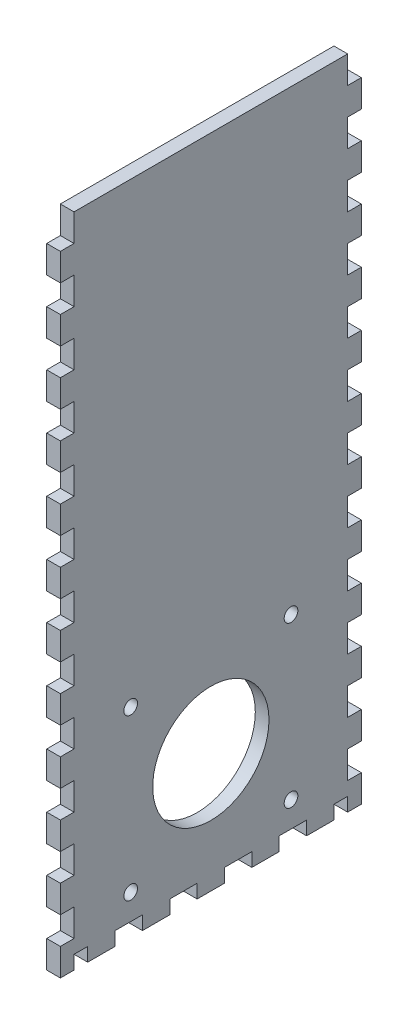
SolidWorks part; units mm, degrees
material "Acrylic (Medium-high impact)"
ref_plane "Front Plane" through (0, 0, 0) normal (0, 0, 1) x (1, 0, 0)
ref_plane "Top Plane" through (0, 0, 0) normal (0, 1, 0) x (1, 0, 0)
ref_plane "Right Plane" through (0, 0, 0) normal (1, 0, 0) x (0, 0, -1)
sketch "Sketch1" plane through (0, 0, 0) normal (0, 1, 0) x (1, 0, 0)
  line L1 (-136.525, 69.85) -> (136.525, 69.85)
  line L2 (-136.525, 69.85) -> (-136.525, -69.85)
  line L3 (-136.525, -69.85) -> (136.525, -69.85)
  line L4 (136.525, 69.85) -> (136.525, -69.85)
  point P4 (-136.525, 0)
  point P6 (0, 69.85)
  dimension "D1" = 139.7
  dimension "D2" = 273.05
extrude "Boss-Extrude1" add sketch "Sketch1" along normal blind 6.35
sketch "Sketch2" plane through (0, 6.35, 0) normal (0, 1, 0) x (1, 0, 0)
  line L0 (136.525, -69.85) -> (136.525, 69.85) construction
  line L1 (-136.525, 69.85) -> (136.525, 69.85)
  line L2 (-136.525, 69.85) -> (-136.525, -69.85)
  line L3 (-136.525, -69.85) -> (136.525, -69.85)
  line L4 (136.525, 69.85) -> (136.525, -69.85)
  line L5 (-136.525, -69.85) -> (136.525, -69.85) construction
  line L7 (-130.175, 63.5) -> (130.175, 63.5)
  line L8 (-130.175, 63.5) -> (-130.175, -63.5)
  line L9 (-130.175, -63.5) -> (130.175, -63.5)
  line L10 (130.175, 63.5) -> (130.175, -63.5)
  point P7 (-130.175, 0)
  point P14 (-136.525, 0)
  point P15 (0, -63.5)
  point P16 (0, -69.85)
  point P17 (130.175, 0)
  point P18 (136.525, 0)
  dimension "D1" = 6.35
  dimension "D2" = 6.35
extrude "Boss-Extrude2" add sketch "Sketch2" along normal blind 298.45
sketch "Sketch3" plane through (0, 0, 69.85) normal (0, 0, 1) x (1, 0, 0)
  line L0 (-25.273, 304.8) -> (-25.273, 0) construction
  line L2 (-130.175, 6.35) -> (130.175, 6.35) construction
  line L4 (-28.575, 283.21) -> (-28.575, 6.35)
  line L5 (-28.575, 6.35) -> (-21.971, 6.35)
  line L6 (-21.971, 292.354) -> (-21.971, 6.35)
  line L7 (-21.971, 292.354) -> (-41.529, 292.354)
  line L9 (-31.115, 285.75) -> (-41.529, 285.75)
  line L10 (-41.529, 292.354) -> (-41.529, 285.75)
  line L11 (-21.971, 101.6) -> (-9.271, 101.6) construction
  line L12 (-136.525, 0) -> (136.525, 0) construction
  line L13 (-12.446, 88.9) -> (-12.446, 101.6) construction
  line L14 (-15.621, 88.9) -> (-9.271, 88.9)
  line L15 (-15.621, 88.9) -> (-15.621, 71.9667)
  line L16 (-15.621, 71.9667) -> (-9.271, 71.9667)
  line L17 (-9.271, 88.9) -> (-9.271, 71.9667)
  line L18 (-15.621, 42.3333) -> (-9.271, 42.3333)
  line L19 (-15.621, 42.3333) -> (-15.621, 59.2667)
  line L20 (-15.621, 59.2667) -> (-9.271, 59.2667)
  line L21 (-9.271, 42.3333) -> (-9.271, 59.2667)
  line L26 (-15.621, 29.6333) -> (-9.271, 29.6333)
  line L27 (-15.621, 29.6333) -> (-15.621, 12.7)
  line L28 (-15.621, 12.7) -> (-9.271, 12.7)
  line L29 (-9.271, 29.6333) -> (-9.271, 12.7)
  line L30 (-12.446, 59.2667) -> (-12.446, 71.9667) construction
  line L31 (-12.446, 29.6333) -> (-12.446, 42.3333) construction
  line L32 (-12.446, 12.7) -> (-12.446, 0) construction
  line L33 (-136.525, 304.8) -> (136.525, 304.8) construction
  line L34 (-130.175, 304.8) -> (-130.175, 6.35) construction
  arc A0 (-28.575, 283.21) -> (-31.115, 285.75) centre (-31.115, 283.21) ccw
  point P2 (-65.1597, 304.8)
  point P5 (-25.273, 6.35)
  point P40 (0, 0)
  point P41 (0, 0)
  point P42 (0, 0)
  point P44 (-65.2242, 0)
  point P45 (-69.6985, 0)
  dimension "D5" = 2.54
  dimension "D1" = 6.604
  dimension "D2" = 12.954
  dimension "D3" = 6.604
  dimension "D4" = 286.004
  dimension "D6" = 101.6
  dimension "D7" = 12.7
  dimension "D8" = 12.7
  dimension "D9" = 6.35
  dimension "D10" = 101.6
extrude "Door Slot" cut sketch "Sketch3" against normal blind 12.7
sketch "Sketch4" plane through (0, 0, -63.5) normal (0, 0, 1) x (1, 0, 0)
  line L0 (-136.525, 304.8) -> (136.525, 304.8) construction
  line L1 (-47.879, 304.8) -> (-41.529, 304.8)
  line L2 (-47.879, 304.8) -> (-47.879, 6.35)
  line L3 (-47.879, 6.35) -> (-41.529, 6.35)
  line L4 (-41.529, 304.8) -> (-41.529, 6.35)
  line L5 (-18.796, 263.525) -> (-18.796, 247.65) construction
  line L6 (-41.529, 292.354) -> (-41.529, 285.75) construction
  line L7 (-21.971, 304.8) -> (-15.621, 304.8)
  line L8 (-21.971, 304.8) -> (-21.971, 6.35)
  line L9 (-21.971, 6.35) -> (-15.621, 6.35)
  line L10 (-15.621, 304.8) -> (-15.621, 6.35)
  line L11 (130.175, 6.35) -> (-130.175, 6.35) construction
  line L12 (-21.971, 6.35) -> (-21.971, 292.354) construction
  line L13 (-41.529, 304.8) -> (-47.879, 304.8)
  line L14 (-41.529, 304.8) -> (-41.529, 292.1)
  line L15 (-41.529, 292.1) -> (-47.879, 292.1)
  line L16 (-47.879, 304.8) -> (-47.879, 292.1)
  line L17 (-41.529, 276.225) -> (-47.879, 276.225)
  line L18 (-41.529, 276.225) -> (-41.529, 263.525)
  line L19 (-41.529, 263.525) -> (-47.879, 263.525)
  line L20 (-47.879, 276.225) -> (-47.879, 263.525)
  line L21 (-47.879, 6.35) -> (-41.529, 6.35)
  line L22 (-47.879, 6.35) -> (-47.879, 19.05)
  line L23 (-47.879, 19.05) -> (-41.529, 19.05)
  line L24 (-41.529, 6.35) -> (-41.529, 19.05)
  line L25 (-47.879, 34.925) -> (-41.529, 34.925)
  line L26 (-47.879, 34.925) -> (-47.879, 47.625)
  line L27 (-47.879, 47.625) -> (-41.529, 47.625)
  line L28 (-41.529, 34.925) -> (-41.529, 47.625)
  line L29 (-47.879, 92.075) -> (-41.529, 92.075)
  line L30 (-47.879, 92.075) -> (-47.879, 104.775)
  line L31 (-47.879, 104.775) -> (-41.529, 104.775)
  line L32 (-41.529, 92.075) -> (-41.529, 104.775)
  line L33 (-47.879, 149.225) -> (-41.529, 149.225)
  line L34 (-47.879, 149.225) -> (-47.879, 161.925)
  line L35 (-47.879, 161.925) -> (-41.529, 161.925)
  line L36 (-41.529, 149.225) -> (-41.529, 161.925)
  line L37 (-47.879, 177.8) -> (-41.529, 177.8)
  line L38 (-47.879, 177.8) -> (-47.879, 190.5)
  line L39 (-47.879, 190.5) -> (-41.529, 190.5)
  line L40 (-41.529, 177.8) -> (-41.529, 190.5)
  line L41 (-47.879, 206.375) -> (-41.529, 206.375)
  line L42 (-47.879, 206.375) -> (-47.879, 219.075)
  line L43 (-47.879, 219.075) -> (-41.529, 219.075)
  line L44 (-41.529, 206.375) -> (-41.529, 219.075)
  line L45 (-47.879, 234.95) -> (-41.529, 234.95)
  line L46 (-47.879, 234.95) -> (-47.879, 247.65)
  line L47 (-47.879, 247.65) -> (-41.529, 247.65)
  line L48 (-41.529, 234.95) -> (-41.529, 247.65)
  line L49 (-41.529, 133.35) -> (-47.879, 133.35)
  line L50 (-41.529, 133.35) -> (-41.529, 120.65)
  line L51 (-41.529, 120.65) -> (-47.879, 120.65)
  line L52 (-47.879, 133.35) -> (-47.879, 120.65)
  line L53 (-41.529, 76.2) -> (-47.879, 76.2)
  line L54 (-41.529, 76.2) -> (-41.529, 63.5)
  line L55 (-41.529, 63.5) -> (-47.879, 63.5)
  line L56 (-47.879, 76.2) -> (-47.879, 63.5)
  line L57 (-44.704, 304.8) -> (-44.704, 292.1) construction
  line L58 (-44.704, 292.1) -> (-44.704, 276.225) construction
  line L59 (-44.704, 276.225) -> (-44.704, 263.525) construction
  line L60 (-44.704, 247.65) -> (-44.704, 234.95) construction
  line L61 (-44.704, 234.95) -> (-44.704, 219.075) construction
  line L62 (-44.704, 219.075) -> (-44.704, 206.375) construction
  line L63 (-44.704, 206.375) -> (-44.704, 190.5) construction
  line L64 (-44.704, 190.5) -> (-44.704, 177.8) construction
  line L65 (-44.704, 177.8) -> (-44.704, 161.925) construction
  line L66 (-44.704, 161.925) -> (-44.704, 149.225) construction
  line L67 (-44.704, 133.35) -> (-44.704, 120.65) construction
  line L68 (-44.704, 120.65) -> (-44.704, 104.775) construction
  line L69 (-44.704, 104.775) -> (-44.704, 92.075) construction
  line L70 (-44.704, 92.075) -> (-44.704, 76.2) construction
  line L71 (-44.704, 76.2) -> (-44.704, 63.5) construction
  line L72 (-44.704, 63.5) -> (-44.704, 47.625) construction
  line L73 (-44.704, 47.625) -> (-44.704, 34.925) construction
  line L74 (-44.704, 34.925) -> (-44.704, 19.05) construction
  line L75 (-44.704, 19.05) -> (-44.704, 6.35) construction
  line L76 (-44.704, 149.225) -> (-44.704, 133.35) construction
  line L77 (-44.704, 263.525) -> (-44.704, 247.65) construction
  line L78 (-31.75, 304.8) -> (-31.75, 0) construction
  line L79 (136.525, 304.8) -> (-136.525, 304.8) construction
  line L80 (136.525, 0) -> (-136.525, 0) construction
  line L81 (-31.75, 8.3493) -> (-21.971, 8.3493) construction
  line L82 (-31.75, 8.3493) -> (-41.529, 8.3493) construction
  line L83 (-18.796, 149.225) -> (-18.796, 133.35) construction
  line L84 (-18.796, 19.05) -> (-18.796, 6.35) construction
  line L85 (-18.796, 34.925) -> (-18.796, 19.05) construction
  line L86 (-18.796, 47.625) -> (-18.796, 34.925) construction
  line L87 (-18.796, 63.5) -> (-18.796, 47.625) construction
  line L88 (-18.796, 76.2) -> (-18.796, 63.5) construction
  line L89 (-18.796, 92.075) -> (-18.796, 76.2) construction
  line L90 (-18.796, 104.775) -> (-18.796, 92.075) construction
  line L91 (-18.796, 120.65) -> (-18.796, 104.775) construction
  line L92 (-18.796, 133.35) -> (-18.796, 120.65) construction
  line L93 (-18.796, 161.925) -> (-18.796, 149.225) construction
  line L94 (-18.796, 177.8) -> (-18.796, 161.925) construction
  line L95 (-18.796, 190.5) -> (-18.796, 177.8) construction
  line L96 (-18.796, 206.375) -> (-18.796, 190.5) construction
  line L97 (-18.796, 219.075) -> (-18.796, 206.375) construction
  line L98 (-18.796, 234.95) -> (-18.796, 219.075) construction
  line L99 (-18.796, 247.65) -> (-18.796, 234.95) construction
  line L100 (-18.796, 276.225) -> (-18.796, 263.525) construction
  line L101 (-18.796, 292.1) -> (-18.796, 276.225) construction
  line L102 (-18.796, 304.8) -> (-18.796, 292.1) construction
  line L103 (-15.621, 76.2) -> (-15.621, 63.5)
  line L104 (-21.971, 63.5) -> (-15.621, 63.5)
  line L105 (-21.971, 76.2) -> (-21.971, 63.5)
  line L106 (-21.971, 76.2) -> (-15.621, 76.2)
  line L107 (-15.621, 133.35) -> (-15.621, 120.65)
  line L108 (-21.971, 120.65) -> (-15.621, 120.65)
  line L109 (-21.971, 133.35) -> (-21.971, 120.65)
  line L110 (-21.971, 133.35) -> (-15.621, 133.35)
  line L111 (-21.971, 234.95) -> (-21.971, 247.65)
  line L112 (-15.621, 247.65) -> (-21.971, 247.65)
  line L113 (-15.621, 234.95) -> (-15.621, 247.65)
  line L114 (-15.621, 234.95) -> (-21.971, 234.95)
  line L115 (-21.971, 206.375) -> (-21.971, 219.075)
  line L116 (-15.621, 219.075) -> (-21.971, 219.075)
  line L117 (-15.621, 206.375) -> (-15.621, 219.075)
  line L118 (-15.621, 206.375) -> (-21.971, 206.375)
  line L119 (-21.971, 177.8) -> (-21.971, 190.5)
  line L120 (-15.621, 190.5) -> (-21.971, 190.5)
  line L121 (-15.621, 177.8) -> (-15.621, 190.5)
  line L122 (-15.621, 177.8) -> (-21.971, 177.8)
  line L123 (-21.971, 149.225) -> (-21.971, 161.925)
  line L124 (-15.621, 161.925) -> (-21.971, 161.925)
  line L125 (-15.621, 149.225) -> (-15.621, 161.925)
  line L126 (-15.621, 149.225) -> (-21.971, 149.225)
  line L127 (-21.971, 92.075) -> (-21.971, 104.775)
  line L128 (-15.621, 104.775) -> (-21.971, 104.775)
  line L129 (-15.621, 92.075) -> (-15.621, 104.775)
  line L130 (-15.621, 92.075) -> (-21.971, 92.075)
  line L131 (-21.971, 34.925) -> (-21.971, 47.625)
  line L132 (-15.621, 47.625) -> (-21.971, 47.625)
  line L133 (-15.621, 34.925) -> (-15.621, 47.625)
  line L134 (-15.621, 34.925) -> (-21.971, 34.925)
  line L135 (-21.971, 6.35) -> (-21.971, 19.05)
  line L136 (-15.621, 19.05) -> (-21.971, 19.05)
  line L137 (-15.621, 6.35) -> (-15.621, 19.05)
  line L138 (-15.621, 6.35) -> (-21.971, 6.35)
  line L139 (-15.621, 276.225) -> (-15.621, 263.525)
  line L140 (-21.971, 263.525) -> (-15.621, 263.525)
  line L141 (-21.971, 276.225) -> (-21.971, 263.525)
  line L142 (-21.971, 276.225) -> (-15.621, 276.225)
  line L143 (-15.621, 304.8) -> (-15.621, 292.1)
  line L144 (-21.971, 292.1) -> (-15.621, 292.1)
  line L145 (-21.971, 304.8) -> (-21.971, 292.1)
  line L146 (-21.971, 304.8) -> (-15.621, 304.8)
  line L147 (-21.971, 304.8) -> (-21.971, 6.35)
  line L148 (-15.621, 6.35) -> (-21.971, 6.35)
  line L149 (-15.621, 304.8) -> (-15.621, 6.35)
  line L150 (-15.621, 304.8) -> (-21.971, 304.8)
  point P14 (-41.529, 289.052)
  dimension "D1" = 6.35
  dimension "D2" = 12.7
extrude "Door Guide Holes" cut sketch "Sketch4" against normal up to next contours L17 L4 L15 L2 | L2 L47 L4 L19 | L45 L2 L43 L4 | L41 L2 L39 L4 | L37 L2 L35 L4 | L49 L4 L33 L2 | L4 L51 L2 L31 | L53 L4 L29 L2 | L4 L55 L2 L27 | L25 L2 L23 L4
ref_plane "Plane1" through (-31.75, 0, 0) normal (-1, 0, 0) x (0, 0, 1)
mirror "Mirror1" about plane through (-31.75, 0, 0) normal (-1, 0, 0) of "Door Guide Holes"
sketch "Lever Holes" plane through (0, 0, 69.85) normal (0, 0, 1) x (1, 0, 0)
  line L0 (49.276, 31.75) -> (58.928, 31.75)
  line L1 (49.276, 31.75) -> (49.276, 25.4)
  line L2 (49.276, 25.4) -> (58.928, 25.4)
  line L3 (58.928, 31.75) -> (58.928, 25.4)
  line L4 (36.1315, 19.05) -> (42.4815, 19.05)
  line L5 (36.1315, 19.05) -> (36.1315, 12.7)
  line L6 (36.1315, 12.7) -> (42.4815, 12.7)
  line L7 (42.4815, 19.05) -> (42.4815, 12.7)
  line L8 (65.7225, 19.05) -> (72.0725, 19.05)
  line L9 (65.7225, 19.05) -> (65.7225, 12.7)
  line L10 (65.7225, 12.7) -> (72.0725, 12.7)
  line L11 (72.0725, 19.05) -> (72.0725, 12.7)
  line L12 (42.4815, 15.875) -> (65.7225, 15.875) construction
  line L13 (-136.525, 0) -> (136.525, 0) construction
  line L14 (-21.971, 6.35) -> (130.175, 6.35) construction
  line L15 (130.175, 6.35) -> (-130.175, 6.35) construction
  point P12 (54.102, 15.875)
  point P13 (54.102, 25.4)
  point P14 (39.3065, 12.7)
  point P24 (54.102, 6.35)
  point P25 (0, 0)
  dimension "D1" = 9.652
  dimension "D2" = 6.35
  dimension "D3" = 6.35
  dimension "D4" = 6.35
  dimension "D5" = 23.241
  dimension "D6" = 25.4
  dimension "D7" = 12.7
extrude "Cut-Extrude1" cut sketch "Lever Holes" against normal through all
sketch "Sketch7" plane through (136.525, 0, 0) normal (1, 0, 0) x (0, 0, -1)
  line L0 (-37.211, 92.583) -> (37.211, 92.583)
  line L1 (-37.211, 92.583) -> (-37.211, 18.161)
  line L2 (-37.211, 18.161) -> (37.211, 18.161)
  line L3 (37.211, 92.583) -> (37.211, 18.161)
  line L4 (-69.85, 0) -> (69.85, 0) construction
  circle A0 centre (0, 55.372) radius 26.9875
  circle A1 centre (-37.211, 92.583) radius 3.175
  circle A2 centre (37.211, 92.583) radius 3.175
  circle A3 centre (-37.211, 18.161) radius 3.175
  circle A4 centre (37.211, 18.161) radius 3.175
  point P9 (0, 18.161)
  point P10 (-37.211, 55.372)
  point P12 (43.7877, 25.7461)
  point P15 (0, 0)
  dimension "D3" = 53.975
  dimension "D4" = 6.35
  dimension "D1" = 74.422
  dimension "D2" = 55.372
extrude "Cut-Extrude2" cut sketch "Sketch7" against normal up to next contours A0 | L0 A1 L1 | L1 A1 L0 | L3 A2 L0 | L0 A2 L3 | L2 A3 L1 | L1 A3 L2 | L2 A4 L3 | L3 A4 L2
sketch "Sketch8" plane through (-136.525, 0, 0) normal (-1, 0, 0) x (0, 0, 1)
  line L0 (-69.85, 0) -> (69.85, 0) construction
  circle A0 centre (0, 19.05) radius 3.175
  point P2 (0, 0)
  point P6 (0, 0)
  dimension "D1" = 6.35
  dimension "D2" = 19.05
extrude "Cut-Extrude3" cut sketch "Sketch8" against normal up to next
sketch "Bottom" plane through (0, 0, 0) normal (0, -1, 0) x (1, 0, 0)
  line L0 (-130.175, 63.5) -> (130.175, 63.5) construction
  line L1 (-136.525, 69.85) -> (-122.1539, 69.85)
  line L2 (-136.525, 69.85) -> (-136.525, 63.5)
  line L3 (-136.525, 63.5) -> (-122.1539, 63.5)
  line L4 (-122.1539, 69.85) -> (-122.1539, 63.5)
  line L5 (-122.1539, 69.85) -> (-107.7829, 69.85)
  line L6 (-122.1539, 69.85) -> (-122.1539, 63.5)
  line L7 (-122.1539, 63.5) -> (-107.7829, 63.5)
  line L8 (-107.7829, 69.85) -> (-107.7829, 63.5)
  line L9 (-107.7829, 69.85) -> (-93.4118, 69.85)
  line L10 (-107.7829, 69.85) -> (-107.7829, 63.5)
  line L11 (-107.7829, 63.5) -> (-93.4118, 63.5)
  line L12 (-93.4118, 69.85) -> (-93.4118, 63.5)
  line L13 (-93.4118, 69.85) -> (-79.0408, 69.85)
  line L14 (-93.4118, 69.85) -> (-93.4118, 63.5)
  line L15 (-93.4118, 63.5) -> (-79.0408, 63.5)
  line L16 (-79.0408, 69.85) -> (-79.0408, 63.5)
  line L17 (-136.525, 69.85) -> (136.525, 69.85) construction
  line L18 (-41.529, 63.5) -> (-21.971, 63.5) construction
  line L19 (-79.0408, 69.85) -> (-64.6697, 69.85)
  line L20 (-79.0408, 69.85) -> (-79.0408, 63.5)
  line L21 (-79.0408, 63.5) -> (-64.6697, 63.5)
  line L22 (-64.6697, 69.85) -> (-64.6697, 63.5)
  line L23 (-64.6697, 69.85) -> (-50.2987, 69.85)
  line L24 (-64.6697, 69.85) -> (-64.6697, 63.5)
  line L25 (-64.6697, 63.5) -> (-50.2987, 63.5)
  line L26 (-50.2987, 69.85) -> (-50.2987, 63.5)
  line L27 (-50.2987, 69.85) -> (-35.9276, 69.85)
  line L28 (-50.2987, 69.85) -> (-50.2987, 63.5)
  line L29 (-50.2987, 63.5) -> (-35.9276, 63.5)
  line L30 (-35.9276, 69.85) -> (-35.9276, 63.5)
  line L31 (-35.9276, 69.85) -> (-21.5566, 69.85)
  line L32 (-35.9276, 69.85) -> (-35.9276, 63.5)
  line L33 (-35.9276, 63.5) -> (-21.5566, 63.5)
  line L34 (-21.5566, 69.85) -> (-21.5566, 63.5)
  line L36 (-21.5566, 69.85) -> (-7.1855, 69.85)
  line L37 (-21.5566, 69.85) -> (-21.5566, 63.5)
  line L38 (-21.5566, 63.5) -> (-7.1855, 63.5)
  line L39 (-7.1855, 69.85) -> (-7.1855, 63.5)
  line L40 (-7.1855, 69.85) -> (7.1855, 69.85)
  line L41 (-7.1855, 69.85) -> (-7.1855, 63.5)
  line L42 (-7.1855, 63.5) -> (7.1855, 63.5)
  line L43 (7.1855, 69.85) -> (7.1855, 63.5)
  line L44 (7.1855, 69.85) -> (21.5566, 69.85)
  line L45 (7.1855, 69.85) -> (7.1855, 63.5)
  line L46 (7.1855, 63.5) -> (21.5566, 63.5)
  line L47 (21.5566, 69.85) -> (21.5566, 63.5)
  line L48 (21.5566, 69.85) -> (35.9276, 69.85)
  line L49 (21.5566, 69.85) -> (21.5566, 63.5)
  line L50 (21.5566, 63.5) -> (35.9276, 63.5)
  line L51 (35.9276, 69.85) -> (35.9276, 63.5)
  line L52 (35.9276, 69.85) -> (50.2987, 69.85)
  line L53 (35.9276, 69.85) -> (35.9276, 63.5)
  line L54 (35.9276, 63.5) -> (50.2987, 63.5)
  line L55 (50.2987, 69.85) -> (50.2987, 63.5)
  line L56 (50.2987, 69.85) -> (64.6697, 69.85)
  line L57 (50.2987, 69.85) -> (50.2987, 63.5)
  line L58 (50.2987, 63.5) -> (64.6697, 63.5)
  line L59 (64.6697, 69.85) -> (64.6697, 63.5)
  line L60 (64.6697, 69.85) -> (79.0408, 69.85)
  line L61 (64.6697, 69.85) -> (64.6697, 63.5)
  line L62 (64.6697, 63.5) -> (79.0408, 63.5)
  line L63 (79.0408, 69.85) -> (79.0408, 63.5)
  line L64 (79.0408, 69.85) -> (93.4118, 69.85)
  line L65 (79.0408, 69.85) -> (79.0408, 63.5)
  line L66 (79.0408, 63.5) -> (93.4118, 63.5)
  line L67 (93.4118, 69.85) -> (93.4118, 63.5)
  line L68 (93.4118, 69.85) -> (107.7829, 69.85)
  line L69 (93.4118, 69.85) -> (93.4118, 63.5)
  line L70 (93.4118, 63.5) -> (107.7829, 63.5)
  line L71 (107.7829, 69.85) -> (107.7829, 63.5)
  line L72 (107.7829, 69.85) -> (122.1539, 69.85)
  line L73 (107.7829, 69.85) -> (107.7829, 63.5)
  line L74 (107.7829, 63.5) -> (122.1539, 63.5)
  line L75 (122.1539, 69.85) -> (122.1539, 63.5)
  line L76 (-130.175, -63.5) -> (-130.175, 63.5) construction
  line L77 (-136.525, 69.85) -> (-130.175, 69.85)
  line L78 (-136.525, 69.85) -> (-136.525, 57.15)
  line L79 (-136.525, 57.15) -> (-130.175, 57.15)
  line L80 (-130.175, 69.85) -> (-130.175, 57.15)
  line L82 (-136.525, 57.15) -> (-130.175, 57.15)
  line L83 (-136.525, 57.15) -> (-136.525, 44.45)
  line L84 (-136.525, 44.45) -> (-130.175, 44.45)
  line L85 (-130.175, 57.15) -> (-130.175, 44.45)
  line L86 (-136.525, 44.45) -> (-130.175, 44.45)
  line L87 (-136.525, 44.45) -> (-136.525, 31.75)
  line L88 (-136.525, 31.75) -> (-130.175, 31.75)
  line L89 (-130.175, 44.45) -> (-130.175, 31.75)
  line L90 (-136.525, 31.75) -> (-130.175, 31.75)
  line L91 (-136.525, 31.75) -> (-136.525, 19.05)
  line L92 (-136.525, 19.05) -> (-130.175, 19.05)
  line L93 (-130.175, 31.75) -> (-130.175, 19.05)
  line L94 (-136.525, 19.05) -> (-130.175, 19.05)
  line L95 (-136.525, 19.05) -> (-136.525, 6.35)
  line L96 (-136.525, 6.35) -> (-130.175, 6.35)
  line L97 (-130.175, 19.05) -> (-130.175, 6.35)
  line L98 (-136.525, 6.35) -> (-130.175, 6.35)
  line L99 (-136.525, 6.35) -> (-136.525, -6.35)
  line L100 (-136.525, -6.35) -> (-130.175, -6.35)
  line L101 (-130.175, 6.35) -> (-130.175, -6.35)
  line L102 (-136.525, -6.35) -> (-130.175, -6.35)
  line L103 (-136.525, -6.35) -> (-136.525, -19.05)
  line L104 (-136.525, -19.05) -> (-130.175, -19.05)
  line L105 (-130.175, -6.35) -> (-130.175, -19.05)
  line L106 (-136.525, -19.05) -> (-130.175, -19.05)
  line L107 (-136.525, -19.05) -> (-136.525, -31.75)
  line L108 (-136.525, -31.75) -> (-130.175, -31.75)
  line L109 (-130.175, -19.05) -> (-130.175, -31.75)
  line L110 (-136.525, -31.75) -> (-130.175, -31.75)
  line L111 (-136.525, -31.75) -> (-136.525, -44.45)
  line L112 (-136.525, -44.45) -> (-130.175, -44.45)
  line L113 (-130.175, -31.75) -> (-130.175, -44.45)
  line L114 (-136.525, -44.45) -> (-130.175, -44.45)
  line L115 (-136.525, -44.45) -> (-136.525, -57.15)
  line L116 (-136.525, -57.15) -> (-130.175, -57.15)
  line L117 (-130.175, -44.45) -> (-130.175, -57.15)
  line L118 (136.525, 69.85) -> (136.525, -69.85) construction
  line L119 (122.1539, 69.85) -> (136.525, 69.85)
  line L120 (122.1539, 69.85) -> (122.1539, 63.5)
  line L121 (122.1539, 63.5) -> (136.525, 63.5)
  line L122 (136.525, 69.85) -> (136.525, 63.5)
  line L123 (136.525, -69.85) -> (-136.525, -69.85) construction
  line L124 (-136.525, -57.15) -> (-130.175, -57.15)
  line L125 (-136.525, -57.15) -> (-136.525, -69.85)
  line L126 (-136.525, -69.85) -> (-130.175, -69.85)
  line L127 (-130.175, -57.15) -> (-130.175, -69.85)
  line L128 (150.1775, 0) -> (-150.1775, 0) construction
  line L129 (136.525, -69.85) -> (136.525, -63.5)
  line L130 (122.1539, -63.5) -> (136.525, -63.5)
  line L131 (122.1539, -69.85) -> (136.525, -69.85)
  line L132 (122.1539, -69.85) -> (122.1539, -63.5)
  line L133 (107.7829, -63.5) -> (122.1539, -63.5)
  line L134 (107.7829, -69.85) -> (122.1539, -69.85)
  line L135 (107.7829, -69.85) -> (107.7829, -63.5)
  line L136 (93.4118, -63.5) -> (107.7829, -63.5)
  line L137 (93.4118, -69.85) -> (107.7829, -69.85)
  line L138 (93.4118, -69.85) -> (93.4118, -63.5)
  line L139 (79.0408, -63.5) -> (93.4118, -63.5)
  line L140 (79.0408, -69.85) -> (93.4118, -69.85)
  line L141 (79.0408, -69.85) -> (79.0408, -63.5)
  line L142 (64.6697, -63.5) -> (79.0408, -63.5)
  line L143 (64.6697, -69.85) -> (79.0408, -69.85)
  line L144 (50.2987, -63.5) -> (64.6697, -63.5)
  line L145 (64.6697, -69.85) -> (64.6697, -63.5)
  line L146 (50.2987, -69.85) -> (64.6697, -69.85)
  line L147 (50.2987, -69.85) -> (50.2987, -63.5)
  line L148 (35.9276, -63.5) -> (50.2987, -63.5)
  line L149 (35.9276, -69.85) -> (50.2987, -69.85)
  line L150 (35.9276, -69.85) -> (35.9276, -63.5)
  line L151 (21.5566, -63.5) -> (35.9276, -63.5)
  line L152 (21.5566, -69.85) -> (35.9276, -69.85)
  line L153 (21.5566, -69.85) -> (21.5566, -63.5)
  line L154 (7.1855, -69.85) -> (21.5566, -69.85)
  line L155 (7.1855, -63.5) -> (21.5566, -63.5)
  line L156 (7.1855, -69.85) -> (7.1855, -63.5)
  line L157 (-7.1855, -63.5) -> (7.1855, -63.5)
  line L158 (-7.1855, -69.85) -> (7.1855, -69.85)
  line L159 (-21.5566, -63.5) -> (-7.1855, -63.5)
  line L160 (-7.1855, -69.85) -> (-7.1855, -63.5)
  line L161 (-21.5566, -69.85) -> (-7.1855, -69.85)
  line L162 (-21.5566, -69.85) -> (-21.5566, -63.5)
  line L163 (-35.9276, -63.5) -> (-21.5566, -63.5)
  line L164 (-35.9276, -69.85) -> (-21.5566, -69.85)
  line L165 (-35.9276, -69.85) -> (-35.9276, -63.5)
  line L166 (-50.2987, -63.5) -> (-35.9276, -63.5)
  line L167 (-50.2987, -69.85) -> (-35.9276, -69.85)
  line L168 (-50.2987, -69.85) -> (-50.2987, -63.5)
  line L169 (-64.6697, -69.85) -> (-50.2987, -69.85)
  line L170 (-64.6697, -63.5) -> (-50.2987, -63.5)
  line L171 (-79.0408, -63.5) -> (-64.6697, -63.5)
  line L172 (-64.6697, -69.85) -> (-64.6697, -63.5)
  line L173 (-79.0408, -69.85) -> (-64.6697, -69.85)
  line L174 (-93.4118, -69.85) -> (-79.0408, -69.85)
  line L175 (-93.4118, -63.5) -> (-79.0408, -63.5)
  line L176 (-79.0408, -69.85) -> (-79.0408, -63.5)
  line L177 (-107.7829, -69.85) -> (-107.7829, -63.5)
  line L178 (-107.7829, -69.85) -> (-93.4118, -69.85)
  line L179 (-93.4118, -69.85) -> (-93.4118, -63.5)
  line L180 (-107.7829, -63.5) -> (-93.4118, -63.5)
  line L181 (-122.1539, -63.5) -> (-107.7829, -63.5)
  line L182 (-122.1539, -69.85) -> (-107.7829, -69.85)
  line L183 (-122.1539, -69.85) -> (-122.1539, -63.5)
  line L184 (-136.525, -69.85) -> (-122.1539, -69.85)
  line L185 (-136.525, -69.85) -> (-136.525, -63.5)
  line L186 (-136.525, -63.5) -> (-122.1539, -63.5)
  line L187 (0, -76.835) -> (0, 76.835) construction
  line L188 (136.525, -69.85) -> (130.175, -69.85)
  line L189 (130.175, -57.15) -> (130.175, -69.85)
  line L190 (136.525, -57.15) -> (136.525, -69.85)
  line L191 (136.525, -57.15) -> (130.175, -57.15)
  line L192 (130.175, -44.45) -> (130.175, -57.15)
  line L193 (136.525, -44.45) -> (136.525, -57.15)
  line L194 (136.525, -44.45) -> (130.175, -44.45)
  line L195 (130.175, -31.75) -> (130.175, -44.45)
  line L196 (136.525, -31.75) -> (136.525, -44.45)
  line L197 (136.525, -31.75) -> (130.175, -31.75)
  line L198 (136.525, -19.05) -> (136.525, -31.75)
  line L199 (130.175, -19.05) -> (130.175, -31.75)
  line L200 (130.175, -6.35) -> (130.175, -19.05)
  line L201 (136.525, -6.35) -> (136.525, -19.05)
  line L202 (136.525, -19.05) -> (130.175, -19.05)
  line L203 (136.525, -6.35) -> (130.175, -6.35)
  line L204 (130.175, 6.35) -> (130.175, -6.35)
  line L205 (136.525, 6.35) -> (136.525, -6.35)
  line L206 (136.525, 6.35) -> (130.175, 6.35)
  line L207 (130.175, 19.05) -> (130.175, 6.35)
  line L208 (136.525, 19.05) -> (136.525, 6.35)
  line L209 (136.525, 19.05) -> (130.175, 19.05)
  line L210 (136.525, 31.75) -> (130.175, 31.75)
  line L211 (136.525, 44.45) -> (130.175, 44.45)
  line L212 (136.525, 57.15) -> (130.175, 57.15)
  line L213 (130.175, 31.75) -> (130.175, 19.05)
  line L214 (136.525, 31.75) -> (136.525, 19.05)
  line L215 (130.175, 44.45) -> (130.175, 31.75)
  line L216 (136.525, 44.45) -> (136.525, 31.75)
  line L217 (130.175, 57.15) -> (130.175, 44.45)
  line L218 (136.525, 57.15) -> (136.525, 44.45)
  line L219 (130.175, 69.85) -> (130.175, 57.15)
  line L220 (136.525, 69.85) -> (136.525, 57.15)
sketch "Front/Back" plane through (0, 0, 69.85) normal (0, 0, 1) x (1, 0, 0)
  line L0 (-130.175, 6.35) -> (-28.575, 6.35) construction
  line L1 (-136.525, 0) -> (-122.1539, 0)
  line L2 (-136.525, 0) -> (-136.525, 6.35)
  line L3 (-136.525, 6.35) -> (-122.1539, 6.35)
  line L4 (-122.1539, 0) -> (-122.1539, 6.35)
  line L5 (-136.525, 0) -> (136.525, 0) construction
  line L6 (-107.7829, 0) -> (-93.4118, 0) construction
  line L7 (-122.1539, 6.35) -> (-107.7829, 6.35)
  line L8 (-122.1539, 6.35) -> (-122.1539, 0)
  line L9 (-122.1539, 0) -> (-107.7829, 0)
  line L10 (-107.7829, 6.35) -> (-107.7829, 0)
  line L11 (-79.0408, 0) -> (-64.6697, 0) construction
  line L12 (-107.7829, 6.35) -> (-93.4118, 6.35)
  line L13 (-107.7829, 6.35) -> (-107.7829, 0)
  line L14 (-107.7829, 0) -> (-93.4118, 0)
  line L15 (-93.4118, 6.35) -> (-93.4118, 0)
  line L16 (-93.4118, 6.35) -> (-79.0408, 6.35)
  line L17 (-93.4118, 6.35) -> (-93.4118, 0)
  line L18 (-93.4118, 0) -> (-79.0408, 0)
  line L19 (-79.0408, 6.35) -> (-79.0408, 0)
  line L20 (-64.6697, 0) -> (-50.2987, 0) construction
  line L21 (-79.0408, 6.35) -> (-64.6697, 6.35)
  line L22 (-79.0408, 6.35) -> (-79.0408, 0)
  line L23 (-79.0408, 0) -> (-64.6697, 0)
  line L24 (-64.6697, 6.35) -> (-64.6697, 0)
  line L25 (-64.6697, 6.35) -> (-50.2987, 6.35)
  line L26 (-64.6697, 6.35) -> (-64.6697, 0)
  line L27 (-64.6697, 0) -> (-50.2987, 0)
  line L28 (-50.2987, 6.35) -> (-50.2987, 0)
  line L29 (-50.2987, 0) -> (-35.9276, 0) construction
  line L30 (-50.2987, 6.35) -> (-35.9276, 6.35)
  line L31 (-50.2987, 6.35) -> (-50.2987, 0)
  line L32 (-50.2987, 0) -> (-35.9276, 0)
  line L33 (-35.9276, 6.35) -> (-35.9276, 0)
  line L34 (-21.5566, 0) -> (-7.1855, 0) construction
  line L35 (-35.9276, 6.35) -> (-21.5566, 6.35)
  line L36 (-35.9276, 6.35) -> (-35.9276, 0)
  line L37 (-35.9276, 0) -> (-21.5566, 0)
  line L38 (-21.5566, 6.35) -> (-21.5566, 0)
  line L39 (7.1855, 0) -> (21.5566, 0) construction
  line L40 (-21.5566, 6.35) -> (-7.1855, 6.35)
  line L41 (-21.5566, 6.35) -> (-21.5566, 0)
  line L42 (-21.5566, 0) -> (-7.1855, 0)
  line L43 (-7.1855, 6.35) -> (-7.1855, 0)
  line L44 (-7.1855, 6.35) -> (7.1855, 6.35)
  line L45 (-7.1855, 6.35) -> (-7.1855, 0)
  line L46 (-7.1855, 0) -> (7.1855, 0)
  line L47 (7.1855, 6.35) -> (7.1855, 0)
  line L48 (7.1855, 0) -> (21.5566, 0) construction
  line L49 (35.9276, 0) -> (50.2987, 0) construction
  line L50 (7.1855, 6.35) -> (21.5566, 6.35)
  line L51 (7.1855, 6.35) -> (7.1855, 0)
  line L52 (7.1855, 0) -> (21.5566, 0)
  line L53 (21.5566, 6.35) -> (21.5566, 0)
  line L54 (21.5566, 6.35) -> (35.9276, 6.35)
  line L55 (21.5566, 6.35) -> (21.5566, 0)
  line L56 (21.5566, 0) -> (35.9276, 0)
  line L57 (35.9276, 6.35) -> (35.9276, 0)
  line L58 (64.6697, 0) -> (79.0408, 0) construction
  line L59 (35.9276, 6.35) -> (50.2987, 6.35)
  line L60 (35.9276, 6.35) -> (35.9276, 0)
  line L61 (35.9276, 0) -> (50.2987, 0)
  line L62 (50.2987, 6.35) -> (50.2987, 0)
  line L63 (50.2987, 6.35) -> (64.6697, 6.35)
  line L64 (50.2987, 6.35) -> (50.2987, 0)
  line L65 (50.2987, 0) -> (64.6697, 0)
  line L66 (64.6697, 6.35) -> (64.6697, 0)
  line L67 (50.2987, 0) -> (64.6697, 0) construction
  line L68 (93.4118, 0) -> (107.7829, 0) construction
  line L69 (64.6697, 6.35) -> (79.0408, 6.35)
  line L70 (64.6697, 6.35) -> (64.6697, 0)
  line L71 (64.6697, 0) -> (79.0408, 0)
  line L72 (79.0408, 6.35) -> (79.0408, 0)
  line L73 (79.0408, 6.35) -> (93.4118, 6.35)
  line L74 (79.0408, 6.35) -> (79.0408, 0)
  line L75 (79.0408, 0) -> (93.4118, 0)
  line L76 (93.4118, 6.35) -> (93.4118, 0)
  line L77 (107.7829, 0) -> (122.1539, 0) construction
  line L78 (93.4118, 6.35) -> (107.7829, 6.35)
  line L79 (93.4118, 6.35) -> (93.4118, 0)
  line L80 (93.4118, 0) -> (107.7829, 0)
  line L81 (107.7829, 6.35) -> (107.7829, 0)
  line L82 (107.7829, 0) -> (122.1539, 0) construction
  line L84 (107.7829, 6.35) -> (122.1539, 6.35)
  line L85 (107.7829, 6.35) -> (107.7829, 0)
  line L86 (107.7829, 0) -> (122.1539, 0)
  line L87 (122.1539, 6.35) -> (122.1539, 0)
  line L88 (122.1539, 6.35) -> (136.525, 6.35)
  line L89 (122.1539, 6.35) -> (122.1539, 0)
  line L90 (122.1539, 0) -> (136.525, 0)
  line L91 (136.525, 6.35) -> (136.525, 0)
  line L92 (-130.175, 304.8) -> (-130.175, 6.35) construction
  line L93 (-136.525, 0) -> (-130.175, 0)
  line L94 (-136.525, 0) -> (-136.525, 12.7)
  line L95 (-136.525, 12.7) -> (-130.175, 12.7)
  line L96 (-130.175, 0) -> (-130.175, 12.7)
  line L97 (-136.525, 304.8) -> (-136.525, 0) construction
  line L98 (-136.525, 12.7) -> (-130.175, 12.7)
  line L99 (-136.525, 12.7) -> (-136.525, 25.4)
  line L100 (-136.525, 25.4) -> (-130.175, 25.4)
  line L101 (-130.175, 12.7) -> (-130.175, 25.4)
  line L102 (-136.525, 25.4) -> (-130.175, 25.4)
  line L103 (-136.525, 25.4) -> (-136.525, 38.1)
  line L104 (-136.525, 38.1) -> (-130.175, 38.1)
  line L105 (-130.175, 25.4) -> (-130.175, 38.1)
  line L106 (-136.525, 38.1) -> (-130.175, 38.1)
  line L107 (-136.525, 38.1) -> (-136.525, 50.8)
  line L108 (-136.525, 50.8) -> (-130.175, 50.8)
  line L109 (-130.175, 38.1) -> (-130.175, 50.8)
  line L110 (-136.525, 50.8) -> (-130.175, 50.8)
  line L111 (-136.525, 50.8) -> (-136.525, 63.5)
  line L112 (-136.525, 63.5) -> (-130.175, 63.5)
  line L113 (-130.175, 50.8) -> (-130.175, 63.5)
  line L114 (-136.525, 63.5) -> (-130.175, 63.5)
  line L115 (-136.525, 63.5) -> (-136.525, 76.2)
  line L116 (-136.525, 76.2) -> (-130.175, 76.2)
  line L117 (-130.175, 63.5) -> (-130.175, 76.2)
  line L118 (-136.525, 76.2) -> (-130.175, 76.2)
  line L119 (-136.525, 76.2) -> (-136.525, 88.9)
  line L120 (-136.525, 88.9) -> (-130.175, 88.9)
  line L121 (-130.175, 76.2) -> (-130.175, 88.9)
  line L122 (-136.525, 88.9) -> (-130.175, 88.9)
  line L123 (-136.525, 88.9) -> (-136.525, 101.6)
  line L124 (-136.525, 101.6) -> (-130.175, 101.6)
  line L125 (-130.175, 88.9) -> (-130.175, 101.6)
  line L126 (-136.525, 101.6) -> (-130.175, 101.6)
  line L127 (-136.525, 101.6) -> (-136.525, 114.3)
  line L128 (-136.525, 114.3) -> (-130.175, 114.3)
  line L129 (-130.175, 101.6) -> (-130.175, 114.3)
  line L130 (-136.525, 114.3) -> (-130.175, 114.3)
  line L131 (-136.525, 114.3) -> (-136.525, 127)
  line L132 (-136.525, 127) -> (-130.175, 127)
  line L133 (-130.175, 114.3) -> (-130.175, 127)
  line L134 (-136.525, 127) -> (-130.175, 127)
  line L135 (-136.525, 127) -> (-136.525, 139.7)
  line L136 (-136.525, 139.7) -> (-130.175, 139.7)
  line L137 (-130.175, 127) -> (-130.175, 139.7)
  line L138 (-136.525, 139.7) -> (-130.175, 139.7)
  line L139 (-136.525, 139.7) -> (-136.525, 152.4)
  line L140 (-136.525, 152.4) -> (-130.175, 152.4)
  line L141 (-130.175, 139.7) -> (-130.175, 152.4)
  line L142 (-136.525, 152.4) -> (-130.175, 152.4)
  line L143 (-136.525, 152.4) -> (-136.525, 165.1)
  line L144 (-136.525, 165.1) -> (-130.175, 165.1)
  line L145 (-130.175, 152.4) -> (-130.175, 165.1)
  line L146 (-136.525, 165.1) -> (-130.175, 165.1)
  line L147 (-136.525, 165.1) -> (-136.525, 177.8)
  line L148 (-136.525, 177.8) -> (-130.175, 177.8)
  line L149 (-130.175, 165.1) -> (-130.175, 177.8)
  line L150 (-136.525, 177.8) -> (-130.175, 177.8)
  line L151 (-136.525, 177.8) -> (-136.525, 190.5)
  line L152 (-136.525, 190.5) -> (-130.175, 190.5)
  line L153 (-130.175, 177.8) -> (-130.175, 190.5)
  line L154 (-136.525, 190.5) -> (-130.175, 190.5)
  line L155 (-136.525, 190.5) -> (-136.525, 203.2)
  line L156 (-136.525, 203.2) -> (-130.175, 203.2)
  line L157 (-130.175, 190.5) -> (-130.175, 203.2)
  line L158 (-136.525, 203.2) -> (-130.175, 203.2)
  line L159 (-136.525, 203.2) -> (-136.525, 215.9)
  line L160 (-136.525, 215.9) -> (-130.175, 215.9)
  line L161 (-130.175, 203.2) -> (-130.175, 215.9)
  line L162 (-136.525, 215.9) -> (-130.175, 215.9)
  line L163 (-136.525, 215.9) -> (-136.525, 228.6)
  line L164 (-136.525, 228.6) -> (-130.175, 228.6)
  line L165 (-130.175, 215.9) -> (-130.175, 228.6)
  line L166 (-136.525, 228.6) -> (-130.175, 228.6)
  line L167 (-136.525, 228.6) -> (-136.525, 241.3)
  line L168 (-136.525, 241.3) -> (-130.175, 241.3)
  line L169 (-130.175, 228.6) -> (-130.175, 241.3)
  line L170 (-136.525, 241.3) -> (-130.175, 241.3)
  line L171 (-136.525, 241.3) -> (-136.525, 254)
  line L172 (-136.525, 254) -> (-130.175, 254)
  line L173 (-130.175, 241.3) -> (-130.175, 254)
  line L174 (-136.525, 254) -> (-130.175, 254)
  line L175 (-136.525, 254) -> (-136.525, 266.7)
  line L176 (-136.525, 266.7) -> (-130.175, 266.7)
  line L177 (-130.175, 254) -> (-130.175, 266.7)
  line L178 (-136.525, 266.7) -> (-130.175, 266.7)
  line L179 (-136.525, 266.7) -> (-136.525, 279.4)
  line L180 (-136.525, 279.4) -> (-130.175, 279.4)
  line L181 (-130.175, 266.7) -> (-130.175, 279.4)
  line L182 (-136.525, 279.4) -> (-130.175, 279.4)
  line L183 (-136.525, 279.4) -> (-136.525, 292.1)
  line L184 (-136.525, 292.1) -> (-130.175, 292.1)
  line L185 (-130.175, 279.4) -> (-130.175, 292.1)
  line L186 (-136.525, 292.1) -> (-130.175, 292.1)
  line L187 (-136.525, 292.1) -> (-136.525, 304.8)
  line L188 (-136.525, 304.8) -> (-130.175, 304.8)
  line L189 (-130.175, 292.1) -> (-130.175, 304.8)
  line L190 (-136.525, 304.8) -> (-130.175, 304.8)
  line L194 (-136.525, 304.8) -> (136.525, 304.8) construction
  line L195 (0, -76.835) -> (0, 76.835) construction
  line L196 (136.525, 304.8) -> (130.175, 304.8)
  line L197 (130.175, 292.1) -> (130.175, 304.8)
  line L198 (136.525, 304.8) -> (130.175, 304.8)
  line L199 (136.525, 292.1) -> (136.525, 304.8)
  line L200 (136.525, 292.1) -> (130.175, 292.1)
  line L201 (130.175, 279.4) -> (130.175, 292.1)
  line L202 (136.525, 292.1) -> (130.175, 292.1)
  line L203 (136.525, 279.4) -> (136.525, 292.1)
  line L204 (136.525, 279.4) -> (130.175, 279.4)
  line L205 (130.175, 266.7) -> (130.175, 279.4)
  line L206 (136.525, 279.4) -> (130.175, 279.4)
  line L207 (136.525, 266.7) -> (136.525, 279.4)
  line L208 (136.525, 266.7) -> (130.175, 266.7)
  line L209 (130.175, 254) -> (130.175, 266.7)
  line L210 (136.525, 266.7) -> (130.175, 266.7)
  line L211 (136.525, 254) -> (136.525, 266.7)
  line L212 (136.525, 254) -> (130.175, 254)
  line L213 (130.175, 241.3) -> (130.175, 254)
  line L214 (136.525, 254) -> (130.175, 254)
  line L215 (136.525, 241.3) -> (136.525, 254)
  line L216 (136.525, 241.3) -> (130.175, 241.3)
  line L217 (130.175, 228.6) -> (130.175, 241.3)
  line L218 (136.525, 241.3) -> (130.175, 241.3)
  line L219 (136.525, 228.6) -> (136.525, 241.3)
  line L220 (136.525, 228.6) -> (130.175, 228.6)
  line L221 (130.175, 215.9) -> (130.175, 228.6)
  line L222 (136.525, 228.6) -> (130.175, 228.6)
  line L223 (136.525, 215.9) -> (136.525, 228.6)
  line L224 (136.525, 215.9) -> (130.175, 215.9)
  line L225 (130.175, 203.2) -> (130.175, 215.9)
  line L226 (136.525, 215.9) -> (130.175, 215.9)
  line L227 (136.525, 203.2) -> (136.525, 215.9)
  line L228 (136.525, 203.2) -> (130.175, 203.2)
  line L229 (130.175, 190.5) -> (130.175, 203.2)
  line L230 (136.525, 203.2) -> (130.175, 203.2)
  line L231 (136.525, 190.5) -> (136.525, 203.2)
  line L232 (136.525, 190.5) -> (130.175, 190.5)
  line L233 (130.175, 177.8) -> (130.175, 190.5)
  line L234 (136.525, 190.5) -> (130.175, 190.5)
  line L235 (136.525, 177.8) -> (136.525, 190.5)
  line L236 (136.525, 177.8) -> (130.175, 177.8)
  line L237 (130.175, 165.1) -> (130.175, 177.8)
  line L238 (136.525, 177.8) -> (130.175, 177.8)
  line L239 (136.525, 165.1) -> (136.525, 177.8)
  line L240 (136.525, 165.1) -> (130.175, 165.1)
  line L241 (130.175, 152.4) -> (130.175, 165.1)
  line L242 (136.525, 165.1) -> (130.175, 165.1)
  line L243 (136.525, 152.4) -> (136.525, 165.1)
  line L244 (136.525, 152.4) -> (130.175, 152.4)
  line L245 (130.175, 139.7) -> (130.175, 152.4)
  line L246 (136.525, 152.4) -> (130.175, 152.4)
  line L247 (136.525, 139.7) -> (136.525, 152.4)
  line L248 (136.525, 139.7) -> (130.175, 139.7)
  line L249 (130.175, 127) -> (130.175, 139.7)
  line L250 (136.525, 139.7) -> (130.175, 139.7)
  line L251 (136.525, 127) -> (136.525, 139.7)
  line L252 (136.525, 127) -> (130.175, 127)
  line L253 (130.175, 114.3) -> (130.175, 127)
  line L254 (136.525, 127) -> (130.175, 127)
  line L255 (136.525, 114.3) -> (136.525, 127)
  line L256 (136.525, 114.3) -> (130.175, 114.3)
  line L257 (130.175, 101.6) -> (130.175, 114.3)
  line L258 (136.525, 114.3) -> (130.175, 114.3)
  line L259 (136.525, 101.6) -> (136.525, 114.3)
  line L260 (136.525, 101.6) -> (130.175, 101.6)
  line L261 (130.175, 88.9) -> (130.175, 101.6)
  line L262 (136.525, 101.6) -> (130.175, 101.6)
  line L263 (136.525, 88.9) -> (136.525, 101.6)
  line L264 (136.525, 88.9) -> (130.175, 88.9)
  line L265 (130.175, 76.2) -> (130.175, 88.9)
  line L266 (136.525, 88.9) -> (130.175, 88.9)
  line L267 (136.525, 76.2) -> (136.525, 88.9)
  line L268 (136.525, 76.2) -> (130.175, 76.2)
  line L269 (130.175, 63.5) -> (130.175, 76.2)
  line L270 (136.525, 76.2) -> (130.175, 76.2)
  line L271 (136.525, 63.5) -> (136.525, 76.2)
  line L272 (136.525, 63.5) -> (130.175, 63.5)
  line L273 (130.175, 50.8) -> (130.175, 63.5)
  line L274 (136.525, 63.5) -> (130.175, 63.5)
  line L275 (136.525, 50.8) -> (136.525, 63.5)
  line L276 (136.525, 50.8) -> (130.175, 50.8)
  line L277 (130.175, 38.1) -> (130.175, 50.8)
  line L278 (136.525, 50.8) -> (130.175, 50.8)
  line L279 (136.525, 38.1) -> (136.525, 50.8)
  line L280 (136.525, 38.1) -> (130.175, 38.1)
  line L281 (130.175, 25.4) -> (130.175, 38.1)
  line L282 (136.525, 38.1) -> (130.175, 38.1)
  line L283 (136.525, 25.4) -> (136.525, 38.1)
  line L284 (136.525, 25.4) -> (130.175, 25.4)
  line L285 (130.175, 12.7) -> (130.175, 25.4)
  line L286 (136.525, 25.4) -> (130.175, 25.4)
  line L287 (136.525, 12.7) -> (136.525, 25.4)
  line L288 (136.525, 12.7) -> (130.175, 12.7)
  line L289 (130.175, 0) -> (130.175, 12.7)
  line L290 (136.525, 12.7) -> (130.175, 12.7)
  line L291 (136.525, 0) -> (136.525, 12.7)
  line L292 (136.525, 0) -> (130.175, 0)
  line L293 (136.525, 0) -> (136.525, 6.35)
  point P123 (-136.525, 299.0254)
  point P125 (-130.175, 299.1915)
  point P126 (0, 0)
  point P127 (0, 0)
sketch "Left/Right" plane through (-136.525, 0, 0) normal (-1, 0, 0) x (0, 0, 1)
  line L0 (57.15, 0) -> (44.45, 0) construction
  line L8 (57.15, 0) -> (57.15, 6.35)
  line L9 (57.15, 6.35) -> (44.45, 6.35)
  line L10 (57.15, 6.35) -> (57.15, 0)
  line L11 (57.15, 0) -> (44.45, 0)
  line L12 (44.45, 6.35) -> (44.45, 0)
  line L13 (-69.85, 0) -> (69.85, 0) construction
  line L14 (44.45, 0) -> (31.75, 0) construction
  line L15 (44.45, 6.35) -> (31.75, 6.35)
  line L16 (44.45, 6.35) -> (44.45, 0)
  line L17 (44.45, 0) -> (31.75, 0)
  line L18 (31.75, 6.35) -> (31.75, 0)
  line L19 (31.75, 0) -> (19.05, 0) construction
  line L20 (31.75, 6.35) -> (19.05, 6.35)
  line L21 (31.75, 6.35) -> (31.75, 0)
  line L22 (31.75, 0) -> (19.05, 0)
  line L23 (19.05, 6.35) -> (19.05, 0)
  line L24 (19.05, 0) -> (6.35, 0) construction
  line L25 (19.05, 6.35) -> (6.35, 6.35)
  line L26 (19.05, 6.35) -> (19.05, 0)
  line L27 (19.05, 0) -> (6.35, 0)
  line L28 (6.35, 6.35) -> (6.35, 0)
  line L29 (6.35, 0) -> (-6.35, 0) construction
  line L30 (6.35, 6.35) -> (-6.35, 6.35)
  line L31 (6.35, 6.35) -> (6.35, 0)
  line L32 (6.35, 0) -> (-6.35, 0)
  line L33 (-6.35, 6.35) -> (-6.35, 0)
  line L34 (-6.35, 0) -> (-19.05, 0) construction
  line L35 (-6.35, 6.35) -> (-19.05, 6.35)
  line L36 (-6.35, 6.35) -> (-6.35, 0)
  line L37 (-6.35, 0) -> (-19.05, 0)
  line L38 (-19.05, 6.35) -> (-19.05, 0)
  line L39 (-19.05, 0) -> (-31.75, 0) construction
  line L40 (-19.05, 6.35) -> (-31.75, 6.35)
  line L41 (-19.05, 6.35) -> (-19.05, 0)
  line L42 (-19.05, 0) -> (-31.75, 0)
  line L43 (-31.75, 6.35) -> (-31.75, 0)
  line L44 (-19.05, 0) -> (-31.75, 0) construction
  line L45 (-31.75, 0) -> (-44.45, 0) construction
  line L46 (-31.75, 6.35) -> (-44.45, 6.35)
  line L47 (-31.75, 6.35) -> (-31.75, 0)
  line L48 (-31.75, 0) -> (-44.45, 0)
  line L49 (-44.45, 6.35) -> (-44.45, 0)
  line L50 (69.85, 304.8) -> (69.85, 0) construction
  line L51 (-44.45, 6.35) -> (-57.15, 6.35)
  line L52 (-44.45, 6.35) -> (-44.45, 0)
  line L53 (-44.45, 0) -> (-57.15, 0)
  line L55 (-69.85, 0) -> (-63.5, 0) construction
  line L57 (-57.15, 6.35) -> (-57.15, 0)
  line L60 (-69.85, 0) -> (-63.5, 0) construction
  line L61 (69.85, 0) -> (57.15, 0) construction
  line L63 (-69.85, 6.35) -> (-69.85, 0)
  line L65 (57.15, 6.35) -> (69.85, 6.35)
  line L66 (57.15, 6.35) -> (57.15, 0)
  line L67 (57.15, 0) -> (69.85, 0)
  line L68 (69.85, 6.35) -> (69.85, 0)
  line L69 (69.85, 165.1) -> (69.85, 177.8) construction
  line L70 (63.5, 12.7) -> (69.85, 12.7)
  line L71 (63.5, 12.7) -> (63.5, 25.4)
  line L72 (63.5, 25.4) -> (69.85, 25.4)
  line L73 (-57.15, 0) -> (-69.85, 0)
  line L74 (-69.85, 6.35) -> (-57.15, 6.35)
  line L75 (-57.15, 0) -> (-69.85, 0) construction
  line L76 (69.85, 12.7) -> (69.85, 25.4)
  line L77 (69.85, 0) -> (63.5, 0)
  line L78 (69.85, 0) -> (69.85, 12.7)
  line L79 (69.85, 12.7) -> (63.5, 12.7)
  line L80 (63.5, 0) -> (63.5, 12.7)
  line L81 (63.5, 25.4) -> (69.85, 25.4)
  line L82 (63.5, 25.4) -> (63.5, 38.1)
  line L83 (63.5, 38.1) -> (69.85, 38.1)
  line L84 (69.85, 25.4) -> (69.85, 38.1)
  line L85 (63.5, 38.1) -> (69.85, 38.1)
  line L86 (63.5, 38.1) -> (63.5, 50.8)
  line L87 (63.5, 50.8) -> (69.85, 50.8)
  line L88 (69.85, 38.1) -> (69.85, 50.8)
  line L89 (63.5, 50.8) -> (69.85, 50.8)
  line L90 (63.5, 50.8) -> (63.5, 63.5)
  line L91 (63.5, 63.5) -> (69.85, 63.5)
  line L92 (69.85, 50.8) -> (69.85, 63.5)
  line L93 (63.5, 63.5) -> (69.85, 63.5)
  line L94 (63.5, 63.5) -> (63.5, 76.2)
  line L95 (63.5, 76.2) -> (69.85, 76.2)
  line L96 (69.85, 63.5) -> (69.85, 76.2)
  line L97 (63.5, 76.2) -> (69.85, 76.2)
  line L98 (63.5, 76.2) -> (63.5, 88.9)
  line L99 (63.5, 88.9) -> (69.85, 88.9)
  line L100 (69.85, 76.2) -> (69.85, 88.9)
  line L101 (63.5, 88.9) -> (69.85, 88.9)
  line L102 (63.5, 88.9) -> (63.5, 101.6)
  line L103 (63.5, 101.6) -> (69.85, 101.6)
  line L104 (69.85, 88.9) -> (69.85, 101.6)
  line L105 (63.5, 101.6) -> (69.85, 101.6)
  line L106 (63.5, 101.6) -> (63.5, 114.3)
  line L107 (63.5, 114.3) -> (69.85, 114.3)
  line L108 (69.85, 101.6) -> (69.85, 114.3)
  line L109 (63.5, 114.3) -> (69.85, 114.3)
  line L110 (63.5, 114.3) -> (63.5, 127)
  line L111 (63.5, 127) -> (69.85, 127)
  line L112 (69.85, 114.3) -> (69.85, 127)
  line L113 (63.5, 127) -> (69.85, 127)
  line L114 (63.5, 127) -> (63.5, 139.7)
  line L115 (63.5, 139.7) -> (69.85, 139.7)
  line L116 (69.85, 127) -> (69.85, 139.7)
  line L117 (63.5, 139.7) -> (69.85, 139.7)
  line L118 (63.5, 139.7) -> (63.5, 152.4)
  line L119 (63.5, 152.4) -> (69.85, 152.4)
  line L120 (69.85, 139.7) -> (69.85, 152.4)
  line L121 (63.5, 152.4) -> (69.85, 152.4)
  line L122 (63.5, 152.4) -> (63.5, 165.1)
  line L123 (63.5, 165.1) -> (69.85, 165.1)
  line L124 (69.85, 152.4) -> (69.85, 165.1)
  line L125 (63.5, 165.1) -> (69.85, 165.1)
  line L126 (63.5, 165.1) -> (63.5, 177.8)
  line L127 (63.5, 177.8) -> (69.85, 177.8)
  line L128 (69.85, 165.1) -> (69.85, 177.8)
  line L129 (63.5, 177.8) -> (69.85, 177.8)
  line L130 (63.5, 177.8) -> (63.5, 190.5)
  line L131 (63.5, 190.5) -> (69.85, 190.5)
  line L132 (69.85, 177.8) -> (69.85, 190.5)
  line L133 (69.85, 203.2) -> (69.85, 215.9) construction
  line L134 (63.5, 190.5) -> (69.85, 190.5)
  line L135 (63.5, 190.5) -> (63.5, 203.2)
  line L136 (63.5, 203.2) -> (69.85, 203.2)
  line L137 (69.85, 190.5) -> (69.85, 203.2)
  line L138 (63.5, 203.2) -> (69.85, 203.2)
  line L139 (63.5, 203.2) -> (63.5, 215.9)
  line L140 (63.5, 215.9) -> (69.85, 215.9)
  line L141 (69.85, 203.2) -> (69.85, 215.9)
  line L142 (63.5, 215.9) -> (69.85, 215.9)
  line L143 (63.5, 215.9) -> (63.5, 228.6)
  line L144 (63.5, 228.6) -> (69.85, 228.6)
  line L145 (69.85, 215.9) -> (69.85, 228.6)
  line L146 (69.85, 215.9) -> (69.85, 228.6) construction
  line L147 (63.5, 228.6) -> (69.85, 228.6)
  line L148 (63.5, 228.6) -> (63.5, 241.3)
  line L149 (63.5, 241.3) -> (69.85, 241.3)
  line L150 (69.85, 228.6) -> (69.85, 241.3)
  line L151 (0, -150.1775) -> (0, 150.1775) construction
  line L152 (63.5, 241.3) -> (69.85, 241.3)
  line L153 (63.5, 241.3) -> (63.5, 254)
  line L154 (63.5, 254) -> (69.85, 254)
  line L155 (69.85, 241.3) -> (69.85, 254)
  line L156 (63.5, 254) -> (69.85, 254)
  line L157 (63.5, 254) -> (63.5, 266.7)
  line L158 (63.5, 266.7) -> (69.85, 266.7)
  line L159 (69.85, 254) -> (69.85, 266.7)
  line L160 (63.5, 266.7) -> (69.85, 266.7)
  line L161 (63.5, 266.7) -> (63.5, 279.4)
  line L162 (63.5, 279.4) -> (69.85, 279.4)
  line L163 (69.85, 266.7) -> (69.85, 279.4)
  line L164 (63.5, 279.4) -> (69.85, 279.4)
  line L165 (63.5, 279.4) -> (63.5, 292.1)
  line L166 (63.5, 292.1) -> (69.85, 292.1)
  line L167 (69.85, 279.4) -> (69.85, 292.1)
  line L168 (63.5, 292.1) -> (69.85, 292.1)
  line L169 (63.5, 292.1) -> (63.5, 304.8)
  line L170 (63.5, 304.8) -> (69.85, 304.8)
  line L171 (69.85, 292.1) -> (69.85, 304.8)
  line L172 (-69.85, 292.1) -> (-69.85, 304.8)
  line L173 (-63.5, 304.8) -> (-69.85, 304.8)
  line L174 (-63.5, 292.1) -> (-63.5, 304.8)
  line L175 (-63.5, 292.1) -> (-69.85, 292.1)
  line L176 (-69.85, 279.4) -> (-69.85, 292.1)
  line L177 (-63.5, 292.1) -> (-69.85, 292.1)
  line L178 (-63.5, 279.4) -> (-63.5, 292.1)
  line L179 (-63.5, 279.4) -> (-69.85, 279.4)
  line L180 (-69.85, 266.7) -> (-69.85, 279.4)
  line L181 (-63.5, 279.4) -> (-69.85, 279.4)
  line L182 (-63.5, 266.7) -> (-63.5, 279.4)
  line L183 (-63.5, 266.7) -> (-69.85, 266.7)
  line L184 (-69.85, 254) -> (-69.85, 266.7)
  line L185 (-63.5, 266.7) -> (-69.85, 266.7)
  line L186 (-63.5, 254) -> (-63.5, 266.7)
  line L187 (-63.5, 254) -> (-69.85, 254)
  line L188 (-69.85, 241.3) -> (-69.85, 254)
  line L189 (-63.5, 254) -> (-69.85, 254)
  line L190 (-63.5, 241.3) -> (-63.5, 254)
  line L191 (-63.5, 241.3) -> (-69.85, 241.3)
  line L192 (-69.85, 228.6) -> (-69.85, 241.3)
  line L193 (-63.5, 241.3) -> (-69.85, 241.3)
  line L194 (-63.5, 228.6) -> (-63.5, 241.3)
  line L195 (-63.5, 228.6) -> (-69.85, 228.6)
  line L196 (-69.85, 215.9) -> (-69.85, 228.6)
  line L197 (-63.5, 228.6) -> (-69.85, 228.6)
  line L198 (-63.5, 215.9) -> (-63.5, 228.6)
  line L199 (-63.5, 215.9) -> (-69.85, 215.9)
  line L200 (-69.85, 203.2) -> (-69.85, 215.9)
  line L201 (-63.5, 215.9) -> (-69.85, 215.9)
  line L202 (-63.5, 203.2) -> (-63.5, 215.9)
  line L203 (-63.5, 203.2) -> (-69.85, 203.2)
  line L204 (-69.85, 190.5) -> (-69.85, 203.2)
  line L205 (-63.5, 203.2) -> (-69.85, 203.2)
  line L206 (-63.5, 190.5) -> (-63.5, 203.2)
  line L207 (-63.5, 190.5) -> (-69.85, 190.5)
  line L208 (-69.85, 177.8) -> (-69.85, 190.5)
  line L209 (-63.5, 190.5) -> (-69.85, 190.5)
  line L210 (-63.5, 177.8) -> (-63.5, 190.5)
  line L211 (-63.5, 177.8) -> (-69.85, 177.8)
  line L212 (-69.85, 165.1) -> (-69.85, 177.8)
  line L213 (-63.5, 177.8) -> (-69.85, 177.8)
  line L214 (-63.5, 165.1) -> (-63.5, 177.8)
  line L215 (-63.5, 165.1) -> (-69.85, 165.1)
  line L216 (-69.85, 152.4) -> (-69.85, 165.1)
  line L217 (-63.5, 165.1) -> (-69.85, 165.1)
  line L218 (-63.5, 152.4) -> (-63.5, 165.1)
  line L219 (-63.5, 152.4) -> (-69.85, 152.4)
  line L220 (-69.85, 139.7) -> (-69.85, 152.4)
  line L221 (-63.5, 152.4) -> (-69.85, 152.4)
  line L222 (-63.5, 139.7) -> (-63.5, 152.4)
  line L223 (-63.5, 139.7) -> (-69.85, 139.7)
  line L224 (-69.85, 127) -> (-69.85, 139.7)
  line L225 (-63.5, 139.7) -> (-69.85, 139.7)
  line L226 (-63.5, 127) -> (-63.5, 139.7)
  line L227 (-63.5, 127) -> (-69.85, 127)
  line L228 (-69.85, 114.3) -> (-69.85, 127)
  line L229 (-63.5, 127) -> (-69.85, 127)
  line L230 (-63.5, 114.3) -> (-63.5, 127)
  line L231 (-63.5, 114.3) -> (-69.85, 114.3)
  line L232 (-69.85, 101.6) -> (-69.85, 114.3)
  line L233 (-63.5, 114.3) -> (-69.85, 114.3)
  line L234 (-63.5, 101.6) -> (-63.5, 114.3)
  line L235 (-63.5, 101.6) -> (-69.85, 101.6)
  line L236 (-69.85, 88.9) -> (-69.85, 101.6)
  line L237 (-63.5, 101.6) -> (-69.85, 101.6)
  line L238 (-63.5, 88.9) -> (-63.5, 101.6)
  line L239 (-63.5, 88.9) -> (-69.85, 88.9)
  line L240 (-69.85, 76.2) -> (-69.85, 88.9)
  line L241 (-63.5, 88.9) -> (-69.85, 88.9)
  line L242 (-63.5, 76.2) -> (-63.5, 88.9)
  line L243 (-63.5, 76.2) -> (-69.85, 76.2)
  line L244 (-69.85, 63.5) -> (-69.85, 76.2)
  line L245 (-63.5, 76.2) -> (-69.85, 76.2)
  line L246 (-63.5, 63.5) -> (-63.5, 76.2)
  line L247 (-63.5, 63.5) -> (-69.85, 63.5)
  line L248 (-69.85, 50.8) -> (-69.85, 63.5)
  line L249 (-63.5, 63.5) -> (-69.85, 63.5)
  line L250 (-63.5, 50.8) -> (-63.5, 63.5)
  line L251 (-63.5, 50.8) -> (-69.85, 50.8)
  line L252 (-69.85, 38.1) -> (-69.85, 50.8)
  line L253 (-63.5, 50.8) -> (-69.85, 50.8)
  line L254 (-63.5, 38.1) -> (-63.5, 50.8)
  line L255 (-63.5, 38.1) -> (-69.85, 38.1)
  line L256 (-69.85, 25.4) -> (-69.85, 38.1)
  line L257 (-63.5, 38.1) -> (-69.85, 38.1)
  line L258 (-63.5, 25.4) -> (-63.5, 38.1)
  line L259 (-63.5, 25.4) -> (-69.85, 25.4)
  line L260 (-63.5, 0) -> (-63.5, 12.7)
  line L261 (-69.85, 12.7) -> (-63.5, 12.7)
  line L262 (-69.85, 0) -> (-69.85, 12.7)
  line L263 (-69.85, 0) -> (-63.5, 0)
  line L264 (-69.85, 12.7) -> (-69.85, 25.4)
  line L265 (-63.5, 25.4) -> (-69.85, 25.4)
  line L266 (-63.5, 12.7) -> (-63.5, 25.4)
  line L267 (-63.5, 12.7) -> (-69.85, 12.7)
  line L268 (-69.85, 6.35) -> (-69.85, 0)
  point P58 (63.5, 6.35)
  point P167 (63.5, -19.485)
  point P168 (0, 0)
  line M48 (-69.85, 0) -> (69.85, 0)
  line M49 (69.85, 0) -> (69.85, 304.8)
  line M50 (69.85, 304.8) -> (-69.85, 304.8)
  line M51 (-69.85, 304.8) -> (-69.85, 0)
sketch "Sketch15" plane through (-136.525, 0, 0) normal (-1, 0, 0) x (0, 0, 1)
  line L1 (-63.5, 304.8) -> (88.189, 304.8)
  line L2 (-63.5, 304.8) -> (-63.5, -23.6342)
  line L3 (-63.5, -23.6342) -> (88.189, -23.6342)
  line L4 (88.189, 304.8) -> (88.189, -23.6342)
  point P5 (0, 0)
  point P6 (-69.85, -23.6342)
  point P7 (0, 0)
  point P8 (63.5, 304.8)
  point P10 (0, 0)
  point P11 (88.189, 304.8)
  point P12 (0, 0)
  point P13 (-63.5, 304.8)
sketch "Sketch16" plane through (0, 0, 69.85) normal (0, 0, 1) x (1, 0, 0)
  line L1 (-196.3018, 304.8) -> (130.175, 304.8)
  line L2 (-196.3018, 304.8) -> (-196.3018, -10.4336)
  line L3 (-196.3018, -10.4336) -> (130.175, -10.4336)
  line L4 (130.175, 304.8) -> (130.175, -10.4336)
  point P5 (0, 0)
  point P6 (-196.3018, 306.4036)
  point P7 (130.175, 304.8)
extrude "Cut-Extrude10" cut sketch "Sketch16" against normal through all
extrude "Cut-Extrude11" cut sketch "Left/Right" against normal through all contours L72 L71 L70 M49 | L87 L86 L83 M49 | L95 L94 L91 M49 | L103 L102 L99 M49 | L111 L110 L107 M49 | L119 L118 L115 M49 | L127 L126 L123 M49 | L136 L135 L131 M49 | L144 L143 L140 M49 | L154 L153 L149 M49 | L162 L161 L158 M49 | L169 L166 M49 M50 | L175 L174 M50 M51 | L183 L182 L179 M51 | L191 L190 L187 M51 | L199 L198 L195 M51 | L207 L206 L203 M51 | L215 L214 L211 M51 | L223 L222 L219 M51 | L231 L230 L227 M51 | L239 L238 L235 M51 | L247 L246 L243 M51 | L255 L254 L251 M51 | L261 L266 L259 M51 | L15 L18 L12 M48 | L25 L28 L23 M48 | L35 L38 L33 M48 | L46 L49 L43 M48 | L260 L73 L57 L74 | L80 L65 L8 M48 | L204
